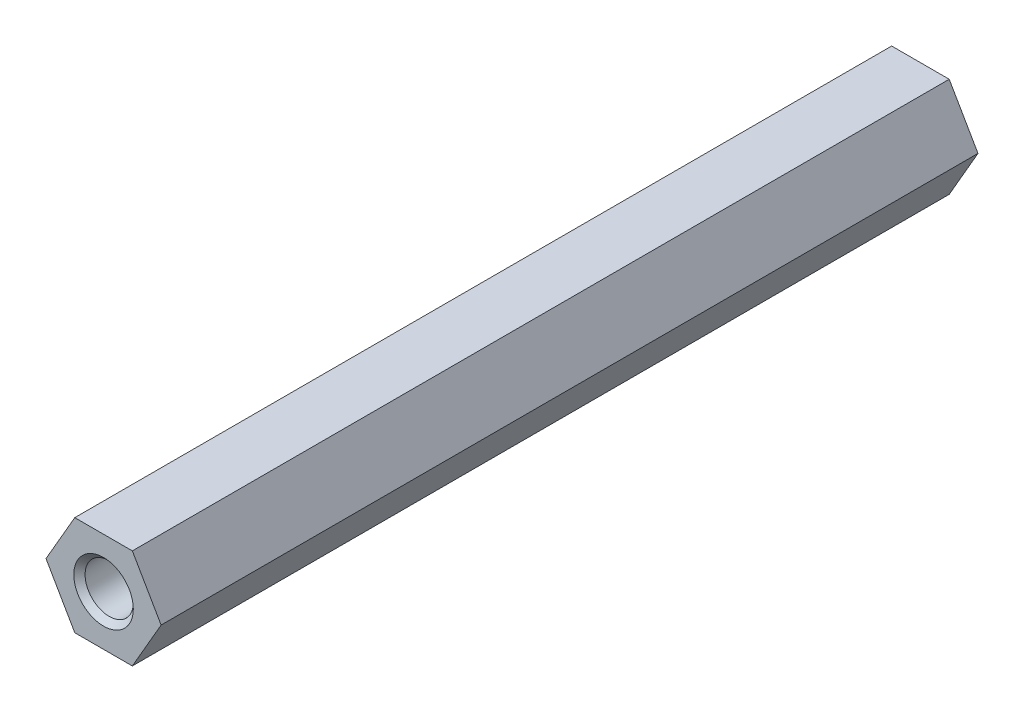
SolidWorks part; units mm, degrees
material "Alloy Steel"
ref_plane "Front Plane" through (0, 0, 0) normal (0, 0, 1) x (1, 0, 0)
ref_plane "Top Plane" through (0, 0, 0) normal (0, 1, 0) x (1, 0, 0)
ref_plane "Right Plane" through (0, 0, 0) normal (1, 0, 0) x (0, 0, -1)
ref_plane "Plane1" through (0, 0, 50.8) normal (0, 0, 1) x (1, 0, 0)
sketch "Sketch1" plane through (0, 0, 50.8) normal (0, 0, 1) x (1, 0, 0)
  line L0 (-3.5796, 0) -> (-1.7898, -3.1)
  line L1 (-1.7898, -3.1) -> (1.7898, -3.1)
  line L2 (1.7898, -3.1) -> (3.5796, 0)
  line L3 (3.5796, 0) -> (1.7898, 3.1)
  line L4 (1.7898, 3.1) -> (-1.7898, 3.1)
  line L5 (-1.7898, 3.1) -> (-3.5796, 0)
extrude "Boss-Extrude1" add sketch "Sketch1" against normal blind 50.8
hole_wizard "Ø3.0 (3) Diameter Hole1" positions "Sketch3" profile "Sketch2" hole size "Ø3.0" standard "ANSI Metric"
sketch "Sketch3" plane through (0, 0, 50.8) normal (0, 0, 1) x (1, 0, 0)
  point P0 (0, 0)
sketch "Sketch2" plane through (0, 0, 50.8) normal (1, 0, 0) x (0, -1, 0)
  line L0 (0, 0) -> (0, 50.8)
  line L1 (0, 50.8) -> (1.5, 50.8)
  line L2 (1.5, 50.8) -> (1.5, 0)
  line L5 (1.5, 0) -> (0, 0)
  line L11 (0, -6.35) -> (0, 107.95) construction
  dimension "Thru Hole Dia." = 3
  dimension "Thru Hole Depth" = 50.8
chamfer "Chamfer1" distance 0.35 angle 45 2 edges at (1.5, 0, 0) (1.5, 0, 50.8)
